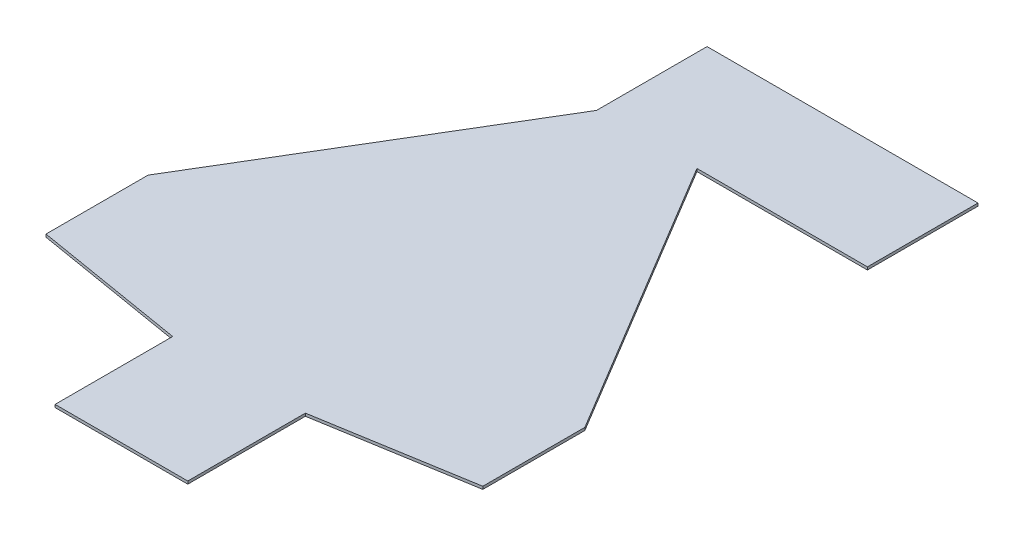
SolidWorks part; units mm, degrees
ref_plane "Front Plane" through (0, 0, 0) normal (0, 0, 1) x (1, 0, 0)
ref_plane "Top Plane" through (0, 0, 0) normal (0, 1, 0) x (1, 0, 0)
ref_plane "Right Plane" through (0, 0, 0) normal (1, 0, 0) x (0, 0, -1)
sketch "Sketch1" plane through (0, 0, 0) normal (0, 1, 0) x (1, 0, 0)
  line L4 (-177.243, -175.2483) -> (-177.243, -269.0134)
  line L6 (23.417, 82.2136) -> (23.417, -298.7864) construction
  line L16 (-22.7315, 183.8136) -> (226.1885, 183.8136)
  line L17 (226.1885, 183.8136) -> (226.1885, 82.2136)
  line L18 (226.1885, 82.2136) -> (69.5655, 82.2136)
  line L21 (224.077, -175.2483) -> (224.077, -269.0134)
  line L22 (69.5655, 82.2136) -> (224.077, -175.2483)
  line L24 (-37.543, -292.3484) -> (-37.543, -400.3864)
  line L27 (-37.543, -400.3864) -> (84.377, -400.3864)
  line L28 (84.377, -400.3864) -> (84.377, -292.3484)
  line L41 (-22.7315, 82.2136) -> (-177.243, -175.2483)
  line L42 (-24.843, 78.6953) -> (-24.843, 171.1136) construction
  line L43 (226.1885, 82.2136) -> (84.377, 82.2136) construction
  line L44 (-24.843, 78.6953) -> (-177.243, -175.2483) construction
  line L45 (-22.7315, 82.2136) -> (-22.7315, 183.8136)
  line L46 (-24.843, 171.1136) -> (213.4885, 171.1136) construction
  line L47 (-22.7315, 82.2136) -> (-30.1373, 82.2136)
  line L48 (61.9438, 94.9136) -> (224.077, -175.2483) construction
  line L49 (213.4885, 94.9136) -> (61.9438, 94.9136) construction
  line L50 (213.4885, 171.1136) -> (213.4885, 94.9136) construction
  line L51 (-37.543, 183.8136) -> (226.1885, 183.8136) construction
  line L52 (-37.543, 82.2136) -> (-37.543, 183.8136) construction
  line L59 (224.077, -269.0134) -> (84.377, -292.3484)
  line L63 (-177.243, -269.0134) -> (-37.543, -292.3484)
  line L66 (-177.243, -175.2483) -> (-177.243, -262.5754) construction
  line L67 (224.077, -175.2483) -> (224.077, -262.5754) construction
  line L68 (84.377, -400.3864) -> (84.377, -298.7864) construction
  line L69 (-37.543, -298.7864) -> (-37.543, -400.3864) construction
  line L70 (-29.0815, 83.9728) -> (-29.0815, 190.1636) construction
  line L71 (-29.0815, 190.1636) -> (232.5385, 190.1636) construction
  line L72 (232.5385, 190.1636) -> (232.5385, 75.8636) construction
  line L73 (232.5385, 75.8636) -> (80.7821, 75.8636) construction
  line L74 (-183.593, -267.9527) -> (-31.193, -293.4091) construction
  line L75 (-189.943, -273.33) -> (-37.543, -298.7864) construction
  line L76 (-31.193, -293.4091) -> (-31.193, -394.0364) construction
  line L77 (236.777, -273.33) -> (84.377, -298.7864) construction
  line L78 (78.027, -394.0364) -> (78.027, -293.4091) construction
  line L79 (-24.843, -288.0318) -> (-24.843, -387.6864) construction
  line L80 (71.677, -387.6864) -> (71.677, -288.0318) construction
  line L81 (-24.843, -387.6864) -> (71.677, -387.6864) construction
  line L82 (-31.193, -394.0364) -> (78.027, -394.0364) construction
  line L83 (230.427, -267.9527) -> (78.027, -293.4091) construction
  line L84 (-29.0815, 83.9728) -> (-183.593, -173.4892) construction
  line L85 (-37.543, 82.2136) -> (-189.943, -171.73) construction
  line L86 (80.7821, 75.8636) -> (230.427, -173.4892) construction
  line L87 (84.377, 82.2136) -> (236.777, -171.73) construction
  line L88 (-177.243, -262.5754) -> (-24.843, -288.0318) construction
  line L89 (224.077, -262.5754) -> (71.677, -288.0318) construction
  line L90 (-183.593, -173.4892) -> (-183.593, -267.9527) construction
  line L91 (-189.943, -171.73) -> (-189.943, -273.33) construction
  line L92 (230.427, -173.4892) -> (230.427, -267.9527) construction
  line L93 (236.777, -171.73) -> (236.777, -273.33) construction
  dimension "D4" = 101.6
  dimension "D9" = 248.92
  dimension "D10" = 12.7
  dimension "D11" = 6.35
extrude "Boss-Extrude1" add sketch "Sketch1" along normal blind 2.54 contours L4 L63 L24 L27 L28 L59 L21 L22 L18 L17 L16 L45 L41
